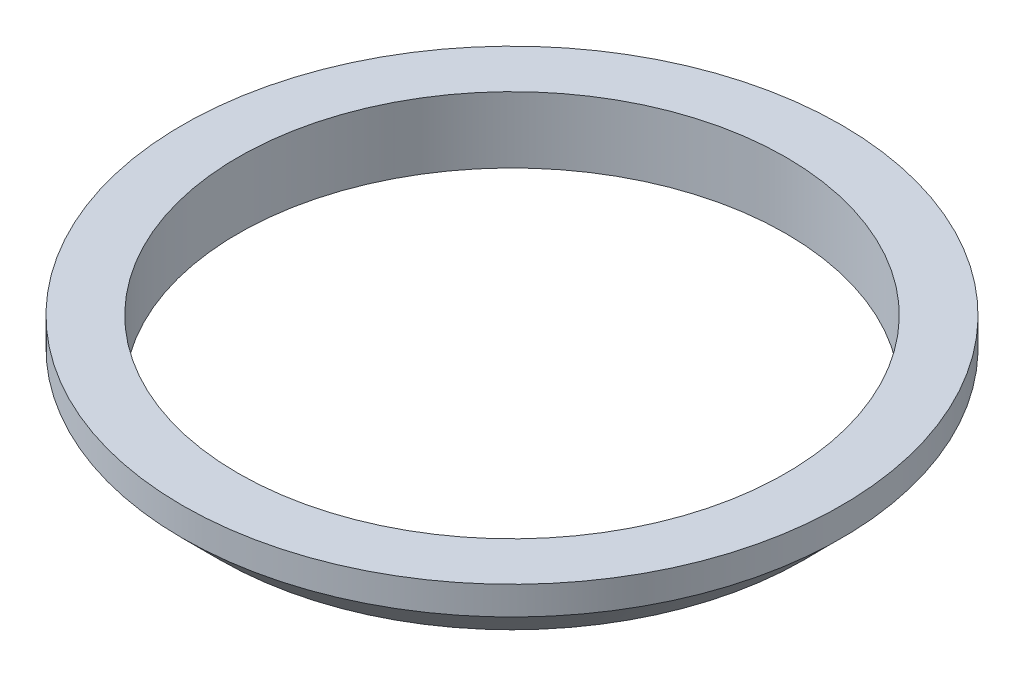
SolidWorks part; units mm, degrees
ref_plane "Plan de face" through (0, 0, 0) normal (0, 0, 1) x (1, 0, 0)
ref_plane "Plan de dessus" through (0, 0, 0) normal (0, 1, 0) x (1, 0, 0)
ref_plane "Plan de droite" through (0, 0, 0) normal (1, 0, 0) x (0, 0, -1)
sketch "Esquisse1" plane through (0, 0, 0) normal (0, 1, 0) x (1, 0, 0)
  circle A0 centre (0, 0) radius 34.9
  circle A1 centre (0, 0) radius 29
  dimension "D1" = 69.8
  dimension "D2" = 58
extrude "Boss.-Extru.1" add sketch "Esquisse1" along normal blind 7
chamfer "Chanfrein1" distance 4 angle 45 1 edges at (0, 0, 34.9)
